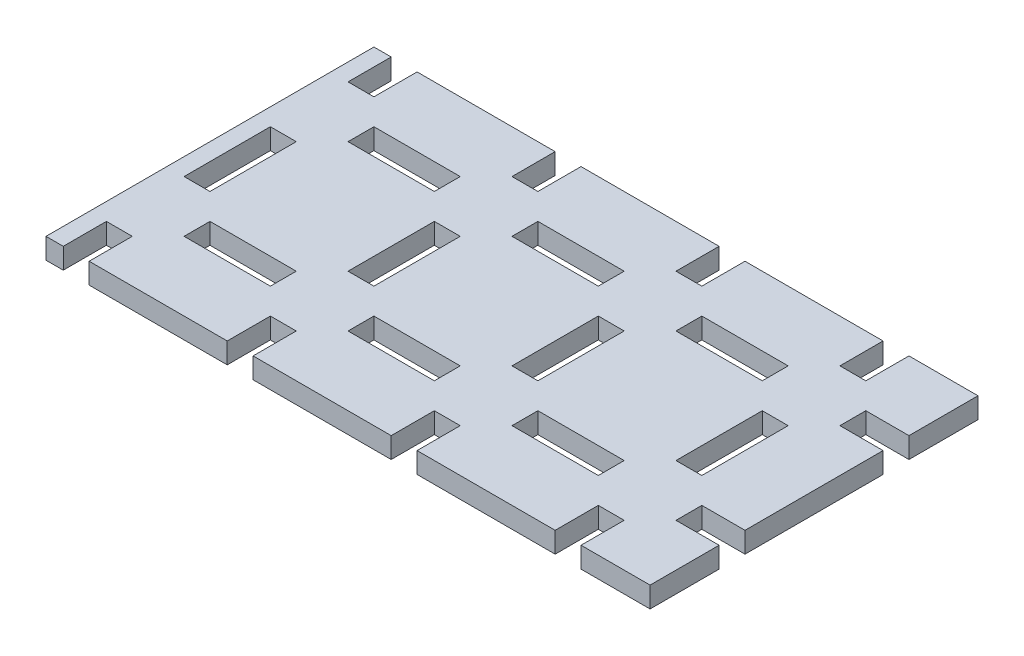
SolidWorks part; units mm, degrees
ref_plane "Plan de face" through (0, 0, 0) normal (0, 0, 1) x (1, 0, 0)
ref_plane "Plan de dessus" through (0, 0, 0) normal (0, 1, 0) x (1, 0, 0)
ref_plane "Plan de droite" through (0, 0, 0) normal (1, 0, 0) x (0, 0, -1)
sketch "Esquisse1" plane through (0, 0, 0) normal (0, 1, 0) x (1, 0, 0)
  line L1 (0, 0) -> (-175, 0)
  line L2 (0, 0) -> (0, -95)
  line L3 (0, -95) -> (-175, -95)
  line L4 (-175, 0) -> (-175, -95)
  dimension "D1" = 175
  dimension "D2" = 95
extrude "Boss.-Extru.1" add sketch "Esquisse1" along normal blind 6
sketch "Esquisse9" plane through (0, 6, 0) normal (0, 1, 0) x (1, 0, 0)
  line L0 (-175, 0) -> (-175, -95) construction
  line L5 (0, -95) -> (0, 0) construction
  line L6 (-155, -20) -> (-130, -20)
  line L7 (-155, -20) -> (-155, -27.5)
  line L8 (-155, -27.5) -> (-130, -27.5)
  line L9 (-130, -20) -> (-130, -27.5)
  line L14 (-155, -67.5) -> (-130, -67.5)
  line L15 (-155, -67.5) -> (-155, -75)
  line L16 (-155, -75) -> (-130, -75)
  line L17 (-130, -67.5) -> (-130, -75)
  line L18 (-107.5, -67.5) -> (-82.5, -67.5)
  line L19 (-107.5, -67.5) -> (-107.5, -75)
  line L20 (-107.5, -75) -> (-82.5, -75)
  line L21 (-82.5, -67.5) -> (-82.5, -75)
  line L22 (-107.5, -20) -> (-82.5, -20)
  line L23 (-107.5, -20) -> (-107.5, -27.5)
  line L24 (-107.5, -27.5) -> (-82.5, -27.5)
  line L25 (-82.5, -20) -> (-82.5, -27.5)
  line L26 (-60, -20) -> (-35, -20)
  line L27 (-60, -20) -> (-60, -27.5)
  line L28 (-60, -27.5) -> (-35, -27.5)
  line L29 (-35, -20) -> (-35, -27.5)
  line L30 (0, -20) -> (-12.5, -20)
  line L31 (0, -20) -> (0, -27.5)
  line L32 (0, -27.5) -> (-12.5, -27.5)
  line L33 (-12.5, -20) -> (-12.5, -27.5)
  line L34 (-175, -95) -> (0, -95) construction
  line L35 (-60, -67.5) -> (-35, -67.5)
  line L36 (-60, -67.5) -> (-60, -75)
  line L37 (-60, -75) -> (-35, -75)
  line L38 (-35, -67.5) -> (-35, -75)
  line L39 (0, -67.5) -> (-12.5, -67.5)
  line L40 (0, -67.5) -> (0, -75)
  line L41 (0, -75) -> (-12.5, -75)
  line L42 (-12.5, -67.5) -> (-12.5, -75)
  line L43 (-170, -95) -> (-162.5, -95)
  line L44 (-170, -95) -> (-170, -82.5)
  line L45 (-170, -82.5) -> (-162.5, -82.5)
  line L46 (-162.5, -95) -> (-162.5, -82.5)
  line L47 (0, 0) -> (-175, 0) construction
  line L48 (-170, -60) -> (-162.5, -60)
  line L49 (-170, -60) -> (-170, -35)
  line L50 (-170, -35) -> (-162.5, -35)
  line L51 (-162.5, -60) -> (-162.5, -35)
  line L52 (-170, 0) -> (-162.5, 0)
  line L53 (-170, 0) -> (-170, -12.5)
  line L54 (-170, -12.5) -> (-162.5, -12.5)
  line L55 (-162.5, 0) -> (-162.5, -12.5)
  line L57 (-122.5, -95) -> (-115, -95)
  line L58 (-122.5, -95) -> (-122.5, -82.5)
  line L59 (-122.5, -82.5) -> (-115, -82.5)
  line L60 (-115, -95) -> (-115, -82.5)
  line L61 (-75, -95) -> (-67.5, -95)
  line L62 (-75, -95) -> (-75, -82.5)
  line L63 (-75, -82.5) -> (-67.5, -82.5)
  line L64 (-67.5, -95) -> (-67.5, -82.5)
  line L65 (-27.5, -95) -> (-20, -95)
  line L66 (-27.5, -95) -> (-27.5, -82.5)
  line L67 (-27.5, -82.5) -> (-20, -82.5)
  line L68 (-20, -95) -> (-20, -82.5)
  line L69 (-122.5, -35) -> (-115, -35)
  line L70 (-122.5, -35) -> (-122.5, -60)
  line L71 (-122.5, -60) -> (-115, -60)
  line L72 (-115, -35) -> (-115, -60)
  line L73 (-75, -35) -> (-67.5, -35)
  line L74 (-75, -35) -> (-75, -60)
  line L75 (-75, -60) -> (-67.5, -60)
  line L76 (-67.5, -35) -> (-67.5, -60)
  line L77 (-27.5, -35) -> (-20, -35)
  line L78 (-27.5, -35) -> (-27.5, -60)
  line L79 (-27.5, -60) -> (-20, -60)
  line L80 (-20, -35) -> (-20, -60)
  line L81 (-122.5, 0) -> (-115, 0)
  line L82 (-122.5, 0) -> (-122.5, -12.5)
  line L83 (-122.5, -12.5) -> (-115, -12.5)
  line L84 (-115, 0) -> (-115, -12.5)
  line L85 (-75, 0) -> (-67.5, 0)
  line L86 (-75, 0) -> (-75, -12.5)
  line L87 (-75, -12.5) -> (-67.5, -12.5)
  line L88 (-67.5, 0) -> (-67.5, -12.5)
  line L89 (-27.5, 0) -> (-20, 0)
  line L90 (-27.5, 0) -> (-27.5, -12.5)
  line L91 (-27.5, -12.5) -> (-20, -12.5)
  line L92 (-20, 0) -> (-20, -12.5)
  point P97 (-107.5, -23.75)
  point P98 (-118.75, -12.5)
  dimension "D3" = 25
  dimension "D4" = 7.5
  dimension "D5" = 12.5
  dimension "D6" = 12.5
  dimension "D7" = 12.5
  dimension "D8" = 12.5
  dimension "D9" = 7.5
  dimension "D10" = 7.5
  dimension "D11" = 7.5
  dimension "D12" = 7.5
  dimension "D13" = 25
  dimension "D14" = 7.5
  dimension "D15" = 25
  dimension "D16" = 7.5
  dimension "D17" = 7.5
  dimension "D18" = 12.5
  dimension "D19" = 25
  dimension "D20" = 7.5
  dimension "D21" = 7.5
  dimension "D22" = 25
  dimension "D23" = 25
  dimension "D24" = 7.5
  dimension "D25" = 7.5
  dimension "D26" = 25
  dimension "D29" = 25
  dimension "D30" = 7.5
  dimension "D31" = 7.5
  dimension "D32" = 25
  dimension "D33" = 25
  dimension "D34" = 7.5
  dimension "D35" = 7.5
  dimension "D36" = 12.5
  dimension "D37" = 7.5
  dimension "D38" = 12.5
  dimension "D39" = 7.5
  dimension "D40" = 12.5
  dimension "D41" = 7.5
  dimension "D42" = 12.5
  dimension "D43" = 7.5
  dimension "D44" = 12.5
  dimension "D45" = 5
  dimension "D46" = 40
  dimension "D47" = 40
  dimension "D48" = 40
  dimension "D51" = 5
  dimension "D52" = 40
  dimension "D53" = 40
  dimension "D54" = 40
  dimension "D55" = 20
  dimension "D56" = 40
  dimension "D57" = 22.5
  dimension "D58" = 5
  dimension "D59" = 20
  dimension "D60" = 40
  dimension "D63" = 40
  dimension "D64" = 20
  dimension "D65" = 40
  dimension "D66" = 22.5
  dimension "D67" = 22.5
  dimension "D68" = 22.5
  dimension "D69" = 40
  dimension "D70" = 22.5
  dimension "D71" = 20
  dimension "D72" = 40
  dimension "D73" = 40
  dimension "D74" = 22.5
  dimension "D75" = 22.5
  dimension "D76" = 22.5
extrude "Enlèv. mat.-Extru.1" cut sketch "Esquisse9" against normal blind 6000
